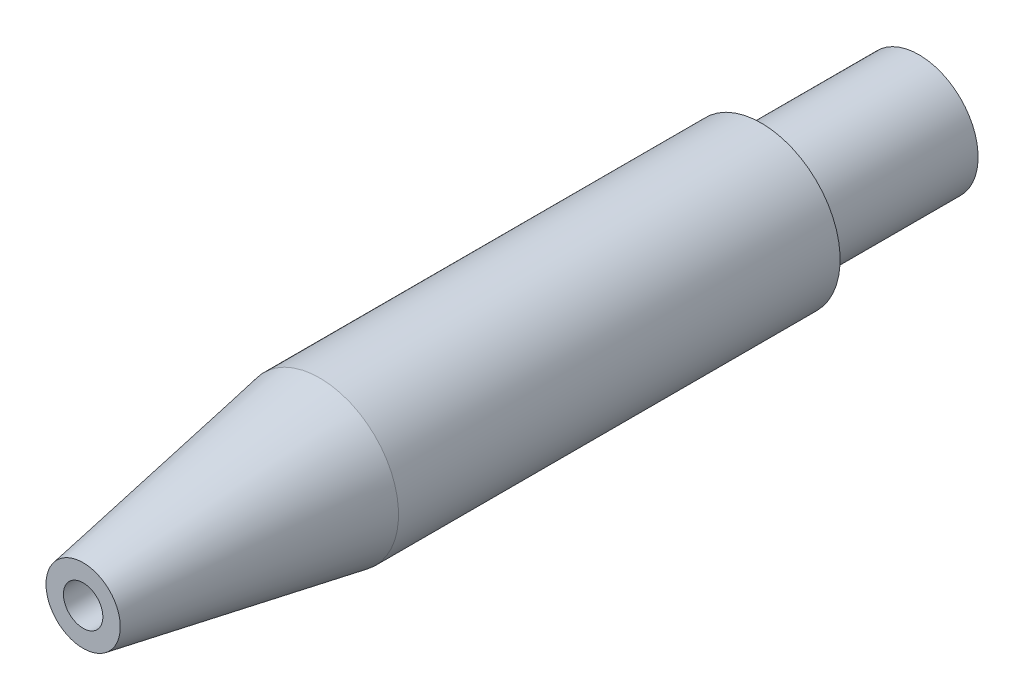
SolidWorks part; units mm, degrees
material "6061 Alloy"
ref_plane "Front Plane" through (0, 0, 0) normal (0, 0, 1) x (1, 0, 0)
ref_plane "Top Plane" through (0, 0, 0) normal (0, 1, 0) x (1, 0, 0)
ref_plane "Right Plane" through (0, 0, 0) normal (1, 0, 0) x (0, 0, -1)
sketch "Sketch1" plane through (0, 0, 0) normal (0, 0, 1) x (1, 0, 0)
  circle A0 centre (0, 0) radius 6.35
  dimension "D1" = 12.7
extrude "Boss-Extrude1" add sketch "Sketch1" along normal blind 67.31
sketch "Sketch7" plane through (0, 0, 0) normal (0, 1, 0) x (1, 0, 0)
  line L0 (6.35, -67.31) -> (6.35, -48.26)
  line L1 (6.35, -67.31) -> (2.991, -67.31)
  line L2 (-6.35, -67.31) -> (6.35, -67.31) construction
  line L8 (6.35, -67.31) -> (6.35, 0) construction
  line L9 (2.991, -67.31) -> (6.35, -48.26)
  line L10 (0, 47.574) -> (0, -47.574) construction
  dimension "D1" = 10
  dimension "D2" = 19.05
revolve "Cut-Revolve1" cut sketch "Sketch7" angle 360 about L10
sketch "Sketch8" plane through (0, 0, 67.31) normal (0, 0, 1) x (1, 0, 0)
  circle A0 centre (0, 0) radius 1.5875
  dimension "D1" = 3.175
extrude "Cut-Extrude1" cut sketch "Sketch8" against normal through all
sketch "Sketch10" plane through (0, 0, 0) normal (0, 0, -1) x (-1, 0, 0)
  circle A0 centre (0, 0) radius 4.7625
  circle A1 centre (0, 0) radius 6.35 construction
  circle A2 centre (0, 0) radius 6.35
  dimension "D1" = 9.525
extrude "Cut-Extrude2" cut sketch "Sketch10" against normal blind 12.7
hole_wizard "1/4 (0.25) Diameter Hole1" positions "3DSketch2" profile "Sketch17" hole size "1/4" standard "ANSI Inch"
sketch3d "3DSketch2"
  point P0 (0, 0, 0)
sketch "Sketch17" plane through (0, 0, 0) normal (1, 0, 0) x (0, 1, 0)
  line L0 (0, 0) -> (0, 61.6511)
  line L1 (0, 61.6511) -> (3.2639, 59.69)
  line L2 (3.2639, 59.69) -> (3.2639, 0)
  line L5 (3.2639, 0) -> (0, 0)
  line L10 (0, 61.6511) -> (-3.2639, 59.69) construction
  line L11 (0, -6.35) -> (0, 107.95) construction
  dimension "Hole Dia." = 6.5278
  dimension "Hole Depth" = 59.69
  dimension "Drill Angle" = 118
